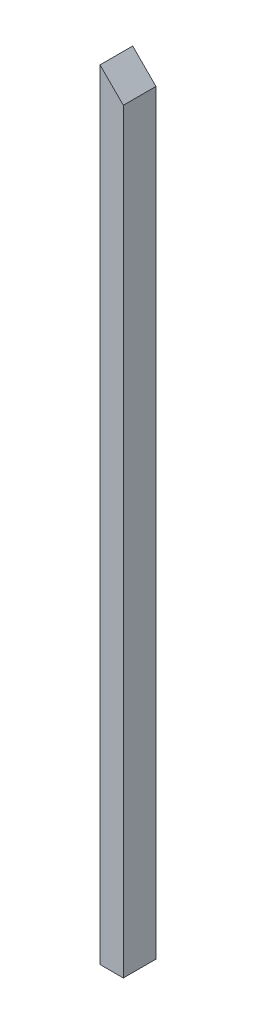
SolidWorks part; units mm, degrees
material "1023 Carbon Steel Sheet (SS)"
ref_plane "Front Plane" through (0, 0, 0) normal (0, 0, 1) x (1, 0, 0)
ref_plane "Top Plane" through (0, 0, 0) normal (0, 1, 0) x (1, 0, 0)
ref_plane "Right Plane" through (0, 0, 0) normal (1, 0, 0) x (0, 0, -1)
sketch "Sketch1" plane through (0, 0, 0) normal (0, 0, 1) x (1, 0, 0)
  line L0 (0, 0) -> (0, 2120.9)
  line L5 (0, 2120.9) -> (63.5, 2057.4)
  line L6 (63.5, 2057.4) -> (63.5, 0)
  line L7 (63.5, 0) -> (0, 0)
  dimension "D1" = 2057.4
  dimension "D2" = 45
  dimension "D3" = 63.5
extrude "Boss-Extrude1" add sketch "Sketch1" along normal blind 88.9
